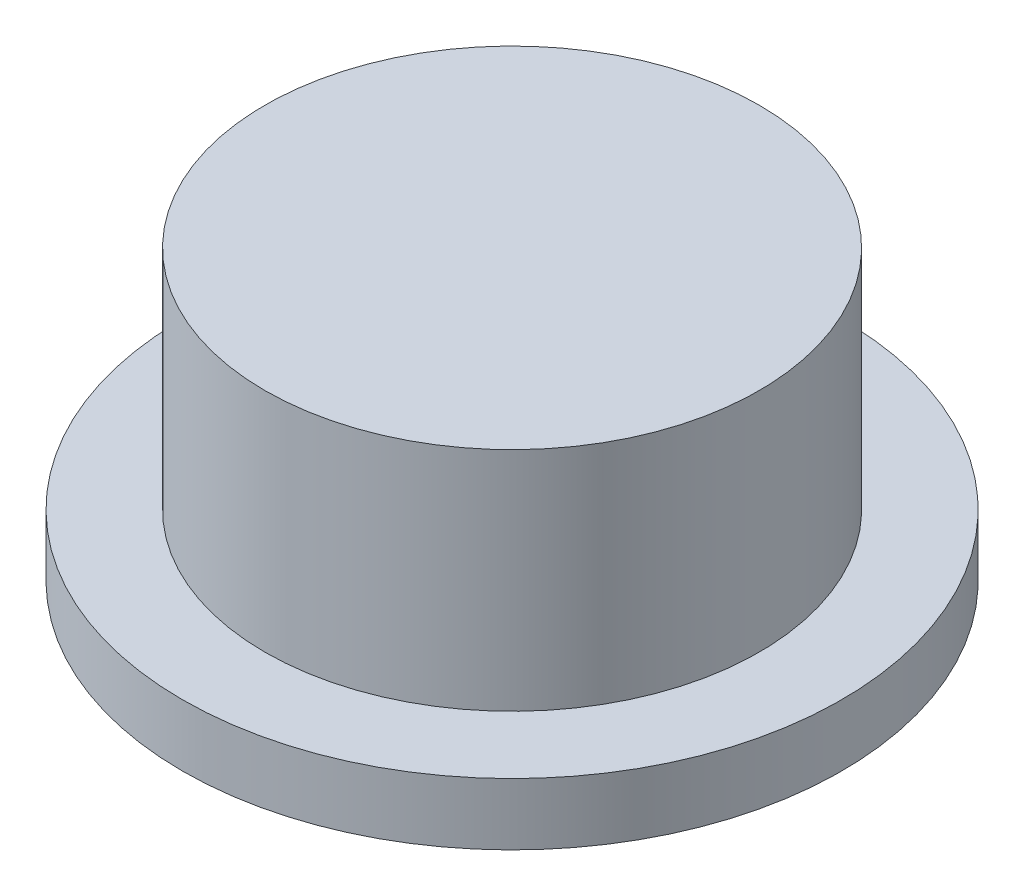
SolidWorks part; units mm, degrees
ref_plane "Front Plane" through (0, 0, 0) normal (0, 0, 1) x (1, 0, 0)
ref_plane "Top Plane" through (0, 0, 0) normal (0, 1, 0) x (1, 0, 0)
ref_plane "Right Plane" through (0, 0, 0) normal (1, 0, 0) x (0, 0, -1)
other "Bounding Box"
ref_plane "Default Plane" through (-8.9266, -12.7485, 0) normal (-0.1736, 0.9848, 0) x (0.9848, 0.1736, 0)
sketch "Sketch1" plane through (0, 0, 0) normal (1, 0, 0) x (0, 0, -1)
  line L0 (-7.8819, -0.9375) -> (-16, -0.9375)
  line L1 (-16, -0.9375) -> (-16, 2.0625)
  line L2 (-16, 2.0625) -> (-12, 2.0625)
  line L3 (-12, 2.0625) -> (-12, 13.0625)
  line L4 (-12, 13.0625) -> (0, 13.0625)
  line L5 (0, 13.0625) -> (0, 0)
  line L6 (0, 0) -> (0, -7.9375)
  line L7 (0, -19.657) -> (0, -41.7062) construction
  arc A0 (-7.8819, -0.9375) -> (0, -7.9375) centre (0, 0) ccw
  dimension "D3" = 7.9375
  dimension "D1" = 24
  dimension "D2" = 32
  dimension "D4" = 21
  dimension "D5" = 14
  dimension "D6" = 3
revolve "Revolve1" add sketch "Sketch1" angle 360 about L7
